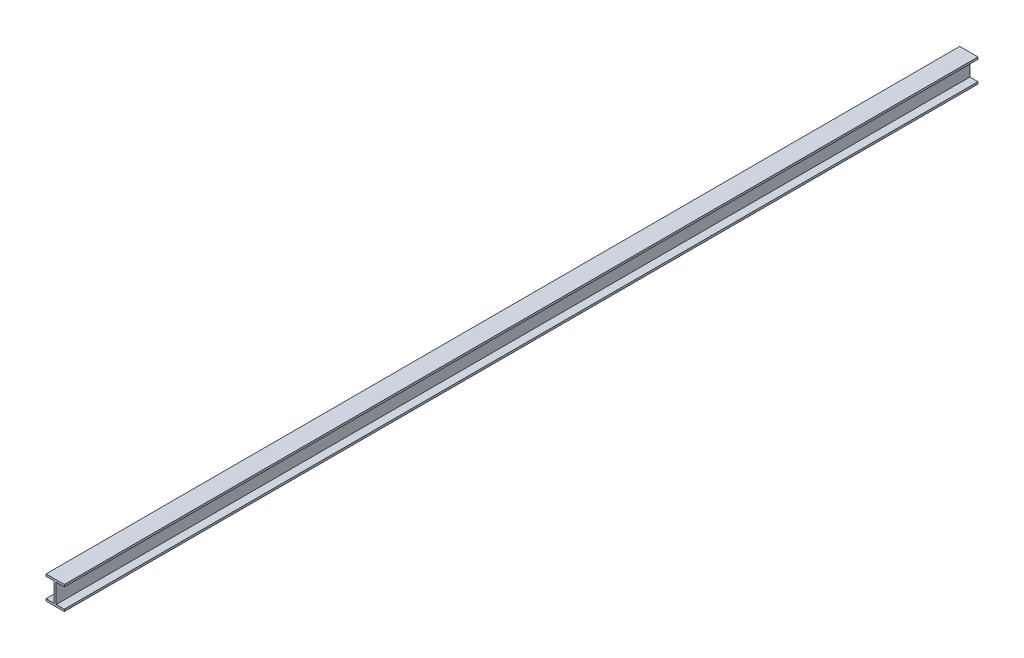
SolidWorks part; units mm, degrees
ref_plane "Front Plane" through (0, 0, 0) normal (0, 0, 1) x (1, 0, 0)
ref_plane "Top Plane" through (0, 0, 0) normal (0, 1, 0) x (1, 0, 0)
ref_plane "Right Plane" through (0, 0, 0) normal (1, 0, 0) x (0, 0, -1)
sketch "Sketch1" plane through (0, 0, 0) normal (0, 0, 1) x (1, 0, 0)
  line L0 (156, -32) -> (280, -32)
  line L1 (0, 0) -> (280, 0)
  line L2 (0, 0) -> (0, -32)
  line L3 (0, -360) -> (280, -360)
  line L4 (280, 0) -> (280, -32)
  line L5 (124, 0) -> (156, 0)
  line L6 (124, -32) -> (124, -328)
  line L7 (124, -360) -> (156, -360)
  line L8 (156, -32) -> (156, -328)
  line L9 (0, 0) -> (280, 0)
  line L10 (0, 0) -> (0, -32)
  line L11 (0, -32) -> (124, -32)
  line L12 (280, 0) -> (280, -32)
  line L13 (0, -360) -> (280, -360)
  line L14 (0, -360) -> (0, -328)
  line L15 (0, -328) -> (124, -328)
  line L16 (280, -360) -> (280, -328)
  line L17 (0, -328) -> (0, -360)
  line L18 (280, -328) -> (280, -360)
  line L19 (156, -328) -> (280, -328)
  dimension "D1" = 280
  dimension "D2" = 360
  dimension "D3" = 32
  dimension "D4" = 32
  dimension "D5" = 124
  dimension "D6" = 124
extrude "Boss-Extrude1" add sketch "Sketch1" along normal blind 14000 contours L19 L8 L0 L4 L1 L2 L11 L6 L15 L14 L3 L16
